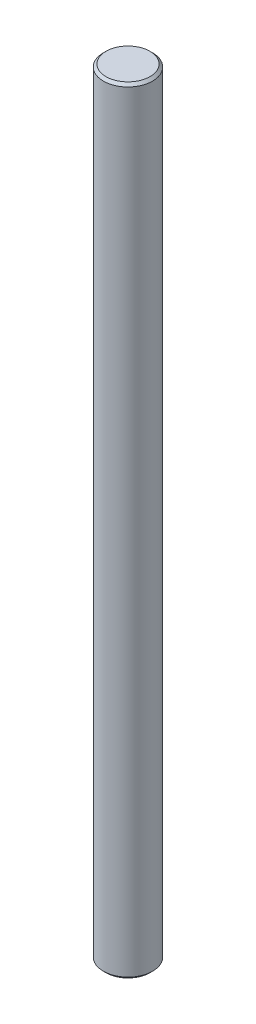
SolidWorks part; units mm, degrees
ref_plane "Front Plane" through (0, 0, 0) normal (0, 0, 1) x (1, 0, 0)
ref_plane "Top Plane" through (0, 0, 0) normal (0, 1, 0) x (1, 0, 0)
ref_plane "Right Plane" through (0, 0, 0) normal (1, 0, 0) x (0, 0, -1)
sketch "Sketch1" plane through (0, 0, 0) normal (0, 1, 0) x (1, 0, 0)
  line L0 (-2.0914, 1.2036) -> (2.0914, 1.2036)
  circle A0 centre (0, 0) radius 2.413
  dimension "D1" = 4.826
extrude "Boss-Extrude1" add sketch "Sketch1" along normal blind 76.2 contours L0 A0 | L0 A0
chamfer "Chamfer1" distance 0.254 angle 45 2 edges at (0, 76.2, 2.413) (0, 0, 2.413)
